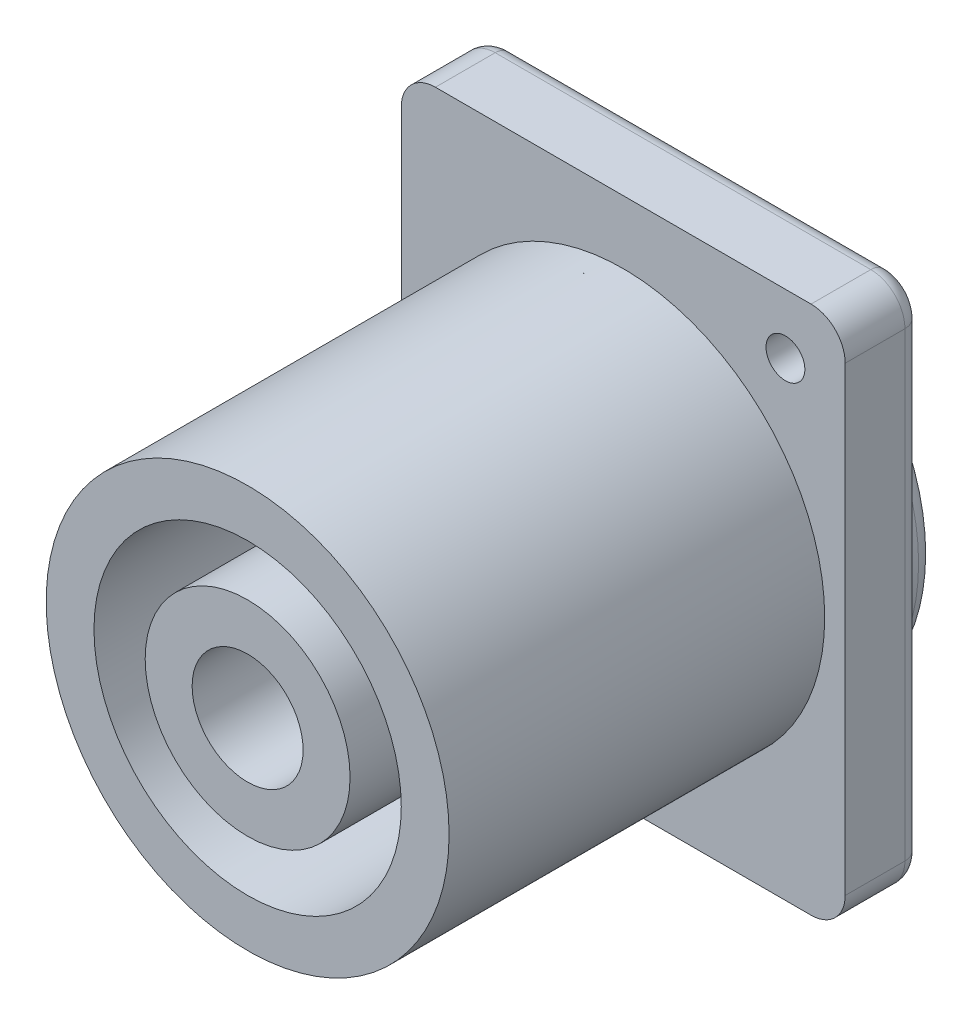
SolidWorks part; units mm, degrees
ref_plane "Plan de face" through (0, 0, 0) normal (0, 0, 1) x (1, 0, 0)
ref_plane "Plan de dessus" through (0, 0, 0) normal (0, 1, 0) x (1, 0, 0)
ref_plane "Plan de droite" through (0, 0, 0) normal (1, 0, 0) x (0, 0, -1)
sketch "Esquisse1" plane through (0, 0, 0) normal (0, 0, 1) x (1, 0, 0)
  line L1 (-19.9365, 11.7379) -> (6.0635, 11.7379)
  line L2 (-19.9365, 11.7379) -> (-19.9365, -19.2621)
  line L3 (-19.9365, -19.2621) -> (6.0635, -19.2621)
  line L4 (6.0635, 11.7379) -> (6.0635, -19.2621)
  circle A0 centre (2.5635, 8.2379) radius 1.1375
  circle A1 centre (-16.4365, -15.7621) radius 1.2353
  dimension "D1" = 26
  dimension "D2" = 31
  dimension "D3" = 3.5
  dimension "D4" = 3.5
  dimension "D5" = 3.5
  dimension "D6" = 3.5
extrude "Boss.-Extru.1" add sketch "Esquisse1" along normal blind 4.5
chamfer "Chanfrein1" distance 1 angle 45 2 edges at (-15.2012, -15.7621, 0) (3.701, 8.2379, 0)
fillet "Congé1" radius 2 4 edges at (6.0635, 11.7379, 2.25) (6.0635, -19.2621, 2.25) (-19.9365, -19.2621, 2.25) (-19.9365, 11.7379, 2.25)
fillet "Congé2" radius 1 8 edges at (5.4777, 11.1521, 0) (6.0635, -3.7621, 0) (5.4777, -18.6763, 0) (-6.9365, -19.2621, 0) (-19.3507, -18.6763, 0) (-19.9365, -3.7621, 0) (-19.3507, 11.1521, 0) (-6.9365, 11.7379, 0)
sketch "Esquisse2" plane through (0, 0, 0) normal (0, 0, -1) x (-1, 0, 0)
  line L0 (-6.0635, -17.2621) -> (-6.0635, 9.7379) construction
  line L1 (-4.0635, 11.7379) -> (17.9365, 11.7379) construction
  circle A0 centre (6.9365, -3.7621) radius 11.8
  point P2 (-6.0635, -3.7621)
  dimension "D3" = 23.6
  dimension "D1" = 13
  dimension "D2" = 15.5
extrude "Boss.-Extru.2" add sketch "Esquisse2" along normal blind 2
fillet "Congé3" radius 1 1 edges at (-18.7365, -3.7621, -2)
sketch "Esquisse3" plane through (0, 0, 4.5) normal (0, 0, 1) x (1, 0, 0)
  line L0 (6.0635, -17.2621) -> (6.0635, 9.7379) construction
  line L1 (4.0635, 11.7379) -> (-17.9365, 11.7379) construction
  circle A0 centre (-6.9365, -3.7621) radius 11.8
  dimension "D2" = 23.6
  dimension "D1" = 13
  dimension "D3" = 15.5
extrude "Boss.-Extru.3" add sketch "Esquisse3" along normal blind 22
sketch "Esquisse4" plane through (0, 0, -2) normal (0, 0, -1) x (-1, 0, 0)
  circle A0 centre (6.9365, -3.7621) radius 9
  circle A1 centre (6.9365, -3.7621) radius 6
  circle A2 centre (6.9365, -3.7621) radius 3.25
  dimension "D1" = 18
  dimension "D2" = 12
  dimension "D3" = 6.5
extrude "Enlèv. mat.-Extru.1" cut sketch "Esquisse4" against normal blind 30 contours A0 A1 | A2
